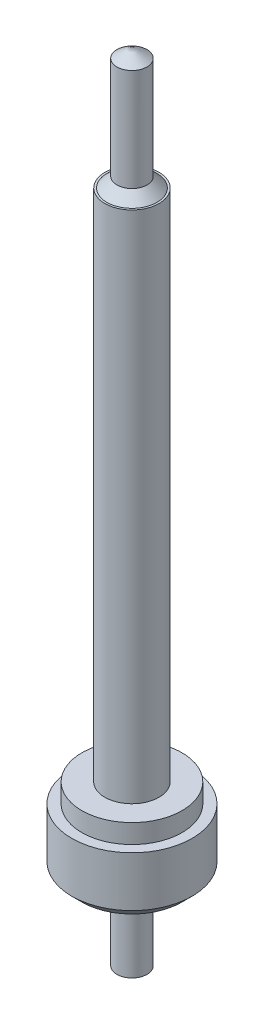
SolidWorks part; units mm, degrees
ref_plane "Alzado" through (0, 0, 0) normal (0, 0, 1) x (1, 0, 0)
ref_plane "Planta" through (0, 0, 0) normal (0, 1, 0) x (1, 0, 0)
ref_plane "Vista lateral" through (0, 0, 0) normal (1, 0, 0) x (0, 0, -1)
sketch "Sketch2" plane through (0, 0, 0) normal (0, 1, 0) x (1, 0, 0)
  circle A0 centre (0, 0) radius 0.3
  dimension "D1" = 0.6
extrude "Boss-Extrude1" add sketch "Sketch2" against normal blind 0.3
sketch "Sketch3" plane through (0, -0.3, 0) normal (0, -1, 0) x (1, 0, 0)
  circle A0 centre (0, 0) radius 0.075
  dimension "D1" = 0.15
extrude "Boss-Extrude2" add sketch "Sketch3" along normal blind 0.45
sketch "Sketch4" plane through (0, 0, 0) normal (0, 1, 0) x (1, 0, 0)
  circle A0 centre (0, 0) radius 0.25
  dimension "D1" = 0.5
extrude "Boss-Extrude3" add sketch "Sketch4" along normal blind 0.095
sketch "Sketch5" plane through (0, 0.095, 0) normal (0, 1, 0) x (1, 0, 0)
  circle A0 centre (0, 0) radius 0.135
  dimension "D1" = 0.27
extrude "Boss-Extrude4" add sketch "Sketch5" along normal blind 2.565
sketch "Sketch6" plane through (0, 2.66, 0) normal (0, 1, 0) x (1, 0, 0)
  circle A0 centre (0, 0) radius 0.075
  dimension "D1" = 0.15
extrude "Boss-Extrude5" add sketch "Sketch6" along normal blind 0.61
chamfer "Chamfer1" distance 0.05 distance2 0.075 1 edges at (0, -0.75, -0.075)
chamfer "Chamfer2" distance 0.05 angle 45 1 edges at (0, -0.3, 0.3)
chamfer "Chamfer3" distance 0.05 angle 45 1 edges at (0, 2.66, 0.075)
chamfer "Chamfer4" distance 0.05 distance2 0.075 1 edges at (0, 3.27, 0.075)
